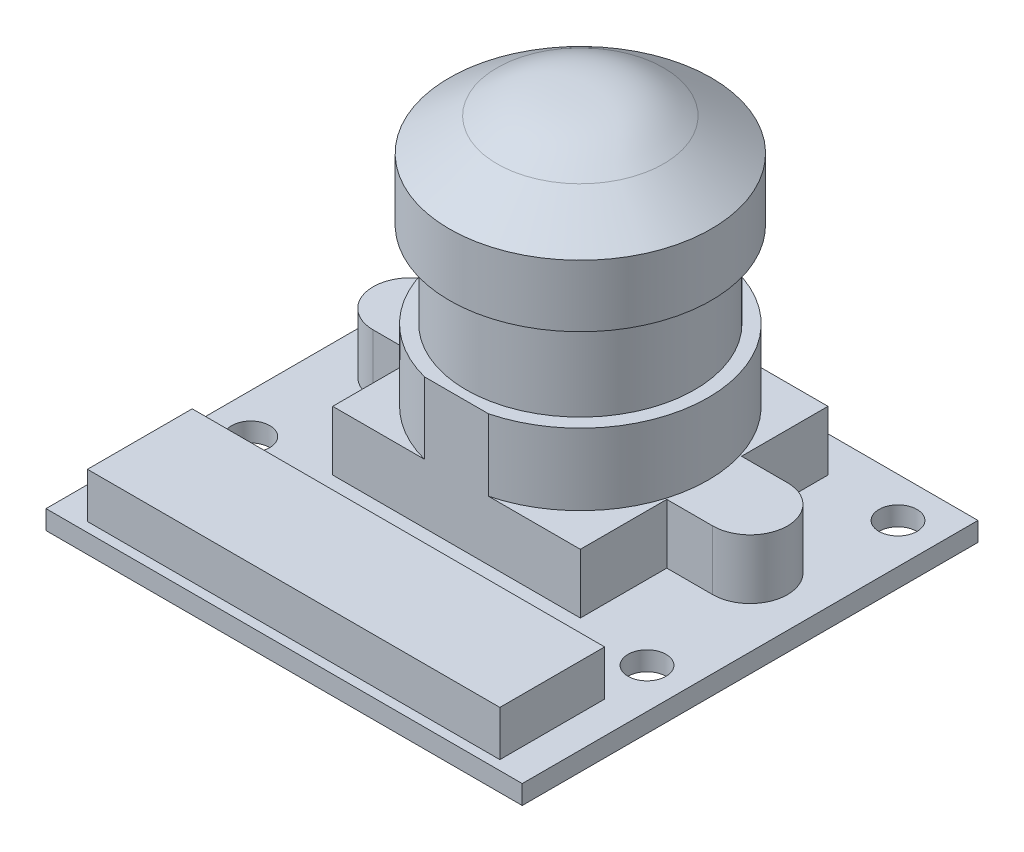
SolidWorks part; units mm, degrees
ref_plane "Front Plane" through (0, 0, 0) normal (0, 0, 1) x (1, 0, 0)
ref_plane "Top Plane" through (0, 0, 0) normal (0, 1, 0) x (1, 0, 0)
ref_plane "Right Plane" through (0, 0, 0) normal (1, 0, 0) x (0, 0, -1)
sketch "Sketch1" plane through (0, 0, 0) normal (0, 1, 0) x (1, 0, 0)
  line L1 (-7.7306, 7.0146) -> (17.6694, 7.0146)
  line L2 (-7.7306, 7.0146) -> (-7.7306, -17.2932)
  line L3 (-7.7306, -17.2932) -> (17.6694, -17.2932)
  line L4 (17.6694, 7.0146) -> (17.6694, -17.2932)
  dimension "D1" = 25.4
  dimension "D2" = 24.3078
extrude "Boss-Extrude1" add sketch "Sketch1" along normal blind 1.016
sketch "Sketch2" plane through (0, 1.016, 0) normal (0, 1, 0) x (1, 0, 0)
  line L0 (-5.597, 5.897) -> (-5.597, 7.0146) construction
  line L1 (17.6694, 7.0146) -> (-7.7306, 7.0146) construction
  line L2 (-6.613, 4.881) -> (-7.7306, 4.881) construction
  line L3 (-7.7306, 7.0146) -> (-7.7306, -17.2932) construction
  line L4 (4.9694, 7.0146) -> (4.9694, -17.2932) construction
  line L5 (-7.7306, -17.2932) -> (17.6694, -17.2932) construction
  line L6 (-5.597, 3.865) -> (-5.597, -7.4888) construction
  line L7 (-5.597, -1.8119) -> (4.7243, -1.8119) construction
  circle A0 centre (-5.597, 4.881) radius 1.016
  circle A1 centre (-5.597, -8.5048) radius 1.016
  circle A2 centre (15.5358, 4.881) radius 1.016
  circle A3 centre (15.5358, -8.5048) radius 1.016
  dimension "D3" = 2.032
  dimension "D1" = 1.1176
  dimension "D2" = 1.1176
  dimension "D4" = 11.3538
extrude "Cut-Extrude1" cut sketch "Sketch2" against normal blind 10
sketch "Sketch3" plane through (0, 1.016, 0) normal (0, 1, 0) x (1, 0, 0)
  line L0 (4.9694, 7.0146) -> (4.9694, -17.2932) construction
  line L1 (17.6694, 7.0146) -> (-7.7306, 7.0146) construction
  line L2 (-7.7306, -17.2932) -> (17.6694, -17.2932) construction
  line L3 (1.863, -16.7852) -> (1.863, -17.2932) construction
  line L4 (15.9676, -16.7852) -> (-6.0288, -16.7852)
  line L5 (15.9676, -16.7852) -> (15.9676, -11.1972)
  line L6 (15.9676, -11.1972) -> (-6.0288, -11.1972)
  line L7 (-6.0288, -16.7852) -> (-6.0288, -11.1972)
  line L8 (15.9676, -16.7852) -> (-6.0288, -11.1972) construction
  line L9 (15.9676, -11.1972) -> (-6.0288, -16.7852) construction
  point P6 (4.9694, -13.9912)
  dimension "D1" = 21.9964
  dimension "D2" = 5.588
  dimension "D3" = 0.508
extrude "Boss-Extrude2" add sketch "Sketch3" along normal blind 2.413
sketch "Sketch4" plane through (0, 1.016, 0) normal (0, 1, 0) x (1, 0, 0)
  line L0 (4.9694, -11.1972) -> (4.9694, 7.0146) construction
  line L1 (15.9676, -11.1972) -> (-6.0288, -11.1972) construction
  line L2 (17.6694, 7.0146) -> (-7.7306, 7.0146) construction
  line L3 (5.4847, 5.1096) -> (5.4847, 7.0146) construction
  line L4 (-1.6346, 5.1096) -> (11.5734, 5.1096)
  line L5 (-1.6346, 5.1096) -> (-1.6346, 0.4995)
  line L6 (-1.6346, -8.0984) -> (11.5734, -8.0984)
  line L7 (11.5734, 5.1096) -> (11.5734, 0.4995)
  line L8 (-1.6346, 5.1096) -> (11.5734, -8.0984) construction
  line L9 (-1.6346, -8.0984) -> (11.5734, 5.1096) construction
  line L10 (16.0184, -1.4944) -> (11.5734, -1.4944) construction
  line L11 (14.0245, -3.4883) -> (11.5734, -3.4883)
  line L12 (14.0245, 0.4995) -> (11.5734, 0.4995)
  line L13 (11.5734, -3.4883) -> (11.5734, -8.0984)
  line L14 (-4.0857, -3.4883) -> (-1.6346, -3.4883)
  line L15 (-4.0857, 0.4995) -> (-1.6346, 0.4995)
  line L16 (-1.6346, -3.4883) -> (-1.6346, -8.0984)
  arc A0 (14.0245, -3.4883) -> (14.0245, 0.4995) centre (14.0245, -1.4944) ccw
  arc A2 (-4.0857, -3.4883) -> (-4.0857, 0.4995) centre (-4.0857, -1.4944) cw
  point P6 (4.9694, -1.4944)
  dimension "D4" = 3.9878
  dimension "D1" = 13.208
  dimension "D2" = 13.208
  dimension "D3" = 1.905
  dimension "D5" = 4.445
extrude "Boss-Extrude3" add sketch "Sketch4" along normal blind 3.175
sketch "Sketch5" plane through (0, 4.191, 0) normal (0, 1, 0) x (1, 0, 0)
  line L0 (4.9694, -8.0984) -> (4.9694, 5.1096) construction
  line L1 (-1.6346, -8.0984) -> (11.5734, -8.0984) construction
  line L2 (11.5734, 5.1096) -> (-1.6346, 5.1096) construction
  line L3 (6.6718, -8.0984) -> (3.267, -8.0984)
  line L4 (4.9694, 5.1096) -> (3.267, 5.1096)
  line L5 (4.9694, 5.1096) -> (6.6718, 5.1096)
  arc A0 (3.267, 5.1096) -> (3.267, -8.0984) centre (4.9694, -1.4944) ccw
  arc A1 (6.6718, -8.0984) -> (6.6718, 5.1096) centre (4.9694, -1.4944) ccw
  dimension "D1" = 13.6398
extrude "Boss-Extrude4" add sketch "Sketch5" along normal blind 3.81
sketch "Sketch6" plane through (0, 8.001, 0) normal (0, 1, 0) x (1, 0, 0)
  circle A0 centre (4.9694, -1.4944) radius 6.0964
extrude "Boss-Extrude5" add sketch "Sketch6" along normal blind 4.572
sketch "Sketch7" plane through (0, 12.573, 0) normal (0, 1, 0) x (1, 0, 0)
  line L0 (11.0658, -1.4944) -> (4.9694, -1.4944) construction
  circle A0 centre (4.9694, -1.4944) radius 6.0964 construction
  circle A1 centre (4.9694, -1.4944) radius 6.0964 construction
ref_plane "Plane1" through (4.9694, 12.573, 1.4944) normal (-1, 0, 0) x (0, 0, 1)
sketch "Sketch8" plane through (4.9694, 12.573, 1.4944) normal (-1, 0, 0) x (0, 0, 1)
  line L0 (0, 0) -> (0, 3.302) construction
  line L1 (6.0964, 0) -> (-6.0964, 0) construction
  line L2 (0, 3.302) -> (-6.985, 3.302) construction
  line L3 (0, 0) -> (0, 6.35) construction
  line L4 (-4.4413, 5.0354) -> (-6.985, 3.302)
  line L5 (0, 6.35) -> (7.1094, 6.35) construction
  line L6 (-1.3223, 6.35) -> (1.3231, 6.35) construction
  line L7 (-6.985, 3.302) -> (-6.985, 0)
  line L8 (-6.985, 0) -> (0, 0)
  line L9 (0, 0) -> (0, 6.35)
  spline S0 degree 3 poles (0, 6.35) (-2.3432, 6.35) (-3.1296, 5.8824) (-4.4413, 5.0354) knots 0 0 0 0 1 1 1 1
  dimension "D1" = 6.985
  dimension "D2" = 3.302
  dimension "D3" = 6.35
revolve "Revolve1" add sketch "Sketch8" angle 360 about L9
sketch "Sketch9" plane through (0, 0, 0) normal (0, -1, 0) x (1, 0, 0)
  line L0 (15.5358, 7.4888) -> (15.5358, -3.865) construction
  line L1 (15.5358, 1.8119) -> (-7.7306, 1.8119) construction
  line L2 (-7.7306, -7.0146) -> (-7.7306, 17.2932) construction
  line L3 (15.993, 1.6595) -> (17.6694, 1.6595) construction
  line L4 (17.6694, 17.2932) -> (17.6694, -7.0146) construction
  line L5 (14.4309, 0.0974) -> (14.4309, -7.0146) construction
  line L6 (17.6694, -7.0146) -> (-7.7306, -7.0146) construction
  line L7 (4.9694, 17.2932) -> (4.9694, -7.0146) construction
  line L8 (-7.7306, 17.2932) -> (17.6694, 17.2932) construction
  circle A0 centre (14.4309, 1.6595) radius 1.5621
  circle A1 centre (15.5358, 8.5048) radius 1.016 construction
  circle A2 centre (15.5358, -4.881) radius 1.016 construction
  circle A3 centre (-4.4921, 1.6595) radius 1.5621
  dimension "D1" = 3.1242
  dimension "D2" = 1.6764
  dimension "D3" = 7.112
extrude "Boss-Extrude6" add sketch "Sketch9" along normal blind 1.0668
fillet "Fillet1" radius 0.25 2 edges at (-4.4921, -1.0668, 3.2216) (14.4309, -1.0668, 0.0974)
sketch "Sketch10" plane through (0, 0, 0) normal (0, -1, 0) x (1, 0, 0)
  circle A0 centre (4.9694, 5.1393) radius 1
extrude "Cut-Extrude2" cut sketch "Sketch10" against normal blind 1
